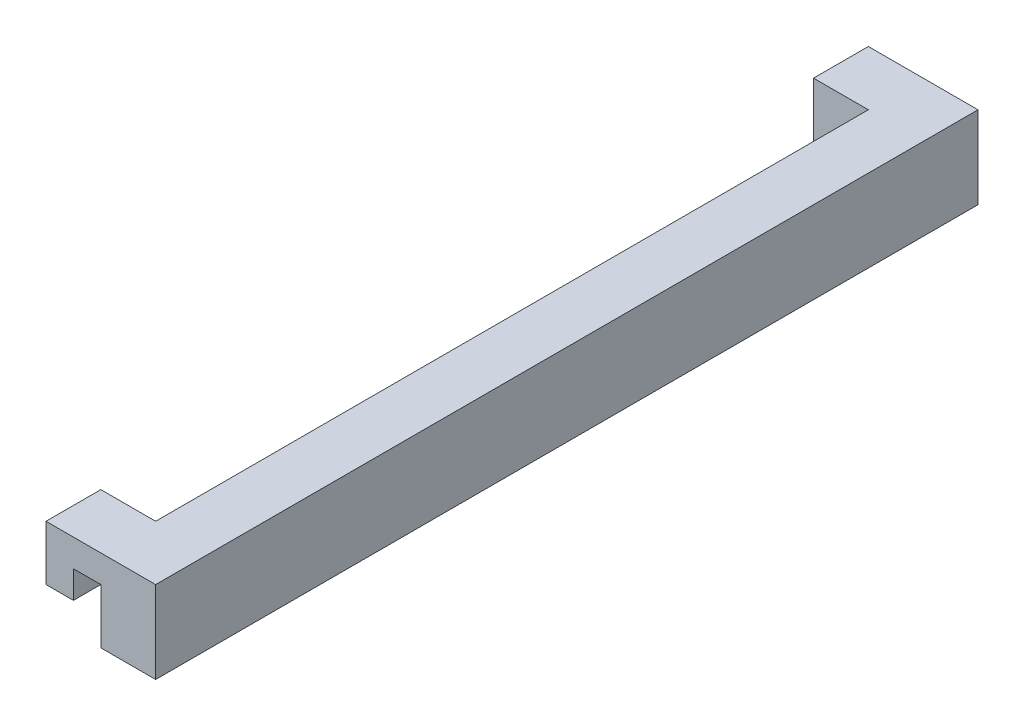
SolidWorks part; units mm, degrees
ref_plane "Front Plane" through (0, 0, 0) normal (0, 0, 1) x (1, 0, 0)
ref_plane "Top Plane" through (0, 0, 0) normal (0, 1, 0) x (1, 0, 0)
ref_plane "Right Plane" through (0, 0, 0) normal (1, 0, 0) x (0, 0, -1)
sketch "Sketch3" plane through (0, 0, 0) normal (0, 1, 0) x (1, 0, 0)
  line L0 (0, 0) -> (0, 20)
  line L1 (0, 20) -> (40, 20)
  line L2 (40, 20) -> (40, -280)
  line L3 (40, -280) -> (0, -280)
  line L4 (0, -280) -> (0, -260)
  line L5 (0, -260) -> (20, -260)
  line L6 (20, -260) -> (20, 0)
  line L7 (20, 0) -> (0, 0)
  dimension "D1" = 20
  dimension "D2" = 40
  dimension "D3" = 20
  dimension "D4" = 300
extrude "Boss-Extrude1" add sketch "Sketch3" along normal blind 30
sketch "Sketch4" plane through (0, 0, 280) normal (0, 0, 1) x (1, 0, 0)
  line L0 (0, 10) -> (10, 10)
  line L1 (0, 30) -> (0, 0) construction
  line L2 (10, 10) -> (10, 20)
  line L3 (10, 20) -> (20, 20)
  line L4 (20, 20) -> (20, 0)
  line L5 (0, 0) -> (40, 0) construction
  line L6 (20, 0) -> (0, 0)
  line L7 (0, 0) -> (0, 10)
  line L8 (20, 30) -> (20, 0) construction
  dimension "D1" = 10
  dimension "D2" = 10
  dimension "D3" = 10
extrude "Cut-Extrude1" cut sketch "Sketch4" against normal through all both and the other way through all
